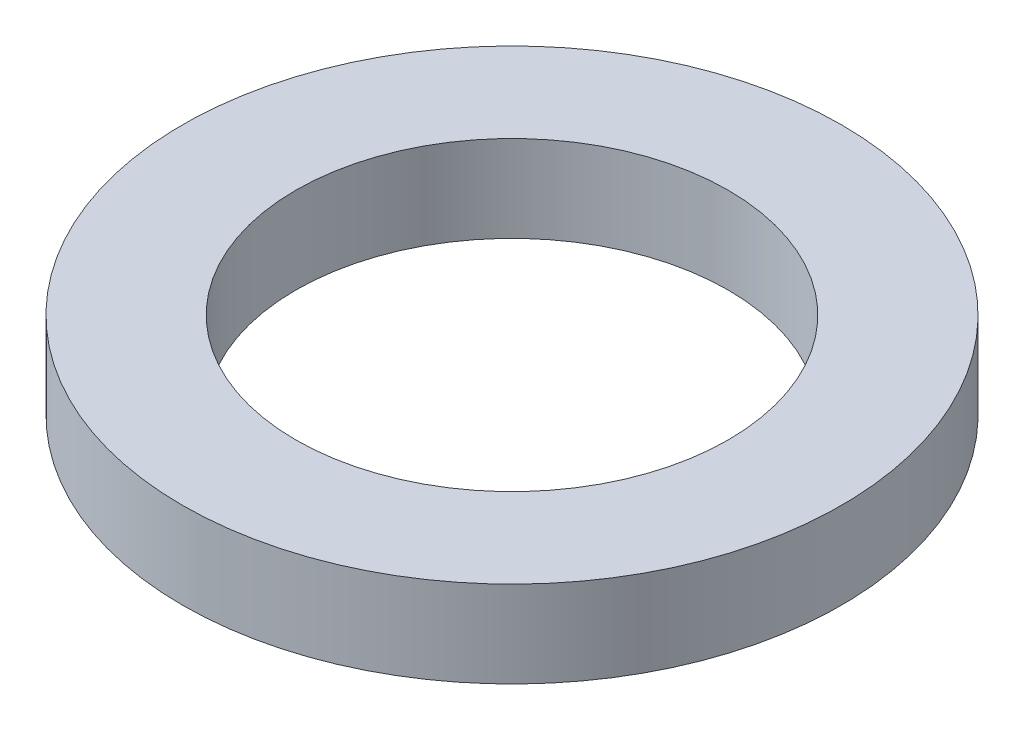
SolidWorks part; units mm, degrees
ref_plane "前视基准面" through (0, 0, 0) normal (0, 0, 1) x (1, 0, 0)
ref_plane "上视基准面" through (0, 0, 0) normal (0, 1, 0) x (1, 0, 0)
ref_plane "右视基准面" through (0, 0, 0) normal (1, 0, 0) x (0, 0, -1)
sketch "草图1" plane through (0, 0, 0) normal (0, 0, 1) x (1, 0, 0)
  line L0 (0, 77.1441) -> (0, -87.8701) construction
  line L1 (-61.6053, 0) -> (62.4304, 0) construction
  line L2 (6.25, 0) -> (6.25, 2.5)
  line L3 (9.525, 0) -> (9.525, 2.5)
  line L4 (6.25, 2.5) -> (9.525, 2.5)
  line L5 (6.25, 0) -> (9.525, 0)
  dimension "D1" = 6.25
  dimension "D2" = 9.525
  dimension "D3" = 2.5
revolve "旋转1" add sketch "草图1" angle 360 about L0
cosmetic thread "装饰螺纹线1" parameters "D2"=13.5
